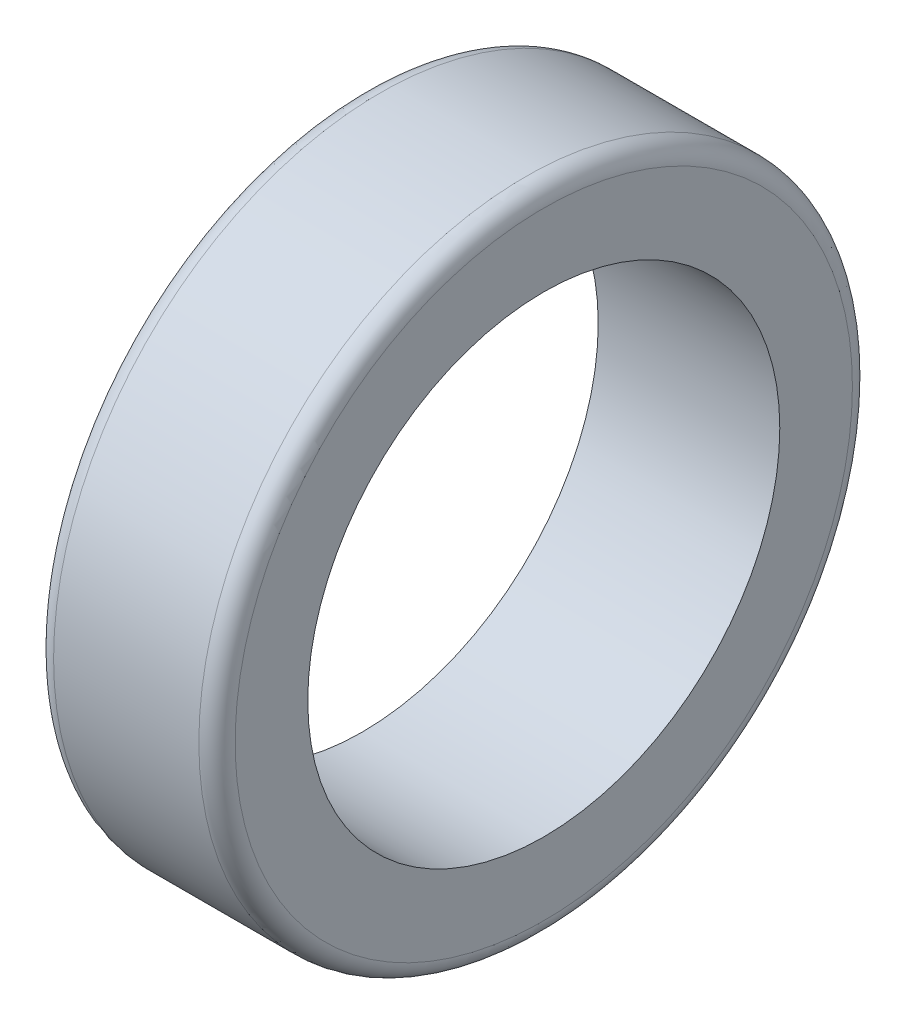
SolidWorks part; units mm, degrees
ref_plane "Front Plane" through (0, 0, 0) normal (0, 0, 1) x (1, 0, 0)
ref_plane "Top Plane" through (0, 0, 0) normal (0, 1, 0) x (1, 0, 0)
ref_plane "Right Plane" through (0, 0, 0) normal (1, 0, 0) x (0, 0, -1)
sketch "Sketch1" plane through (0, 0, 0) normal (0, 0, 1) x (1, 0, 0)
  line L1 (25, -45) -> (-25, -45)
  line L2 (25, -45) -> (25, 40)
  line L3 (20, 45) -> (-20, 45)
  line L4 (-25, -45) -> (-25, 40)
  line L5 (25, -45) -> (-25, 45) construction
  line L6 (25, 45) -> (-25, -45) construction
  arc A0 (-20, 45) -> (-25, 40) centre (-20, 40) ccw
  arc A1 (25, 40) -> (20, 45) centre (20, 40) ccw
  point P0 (0, 0)
  dimension "D3" = 5
  dimension "D1" = 90
  dimension "D2" = 50
revolve "Revolve1" add sketch "Sketch1" angle 360 about L1
sketch "Sketch2" plane through (25, 0, 0) normal (1, 0, 0) x (0, 0, -1)
  circle A0 centre (0, -45) radius 65
  dimension "D1" = 130
extrude "Extrude1" cut sketch "Sketch2" against normal through all
